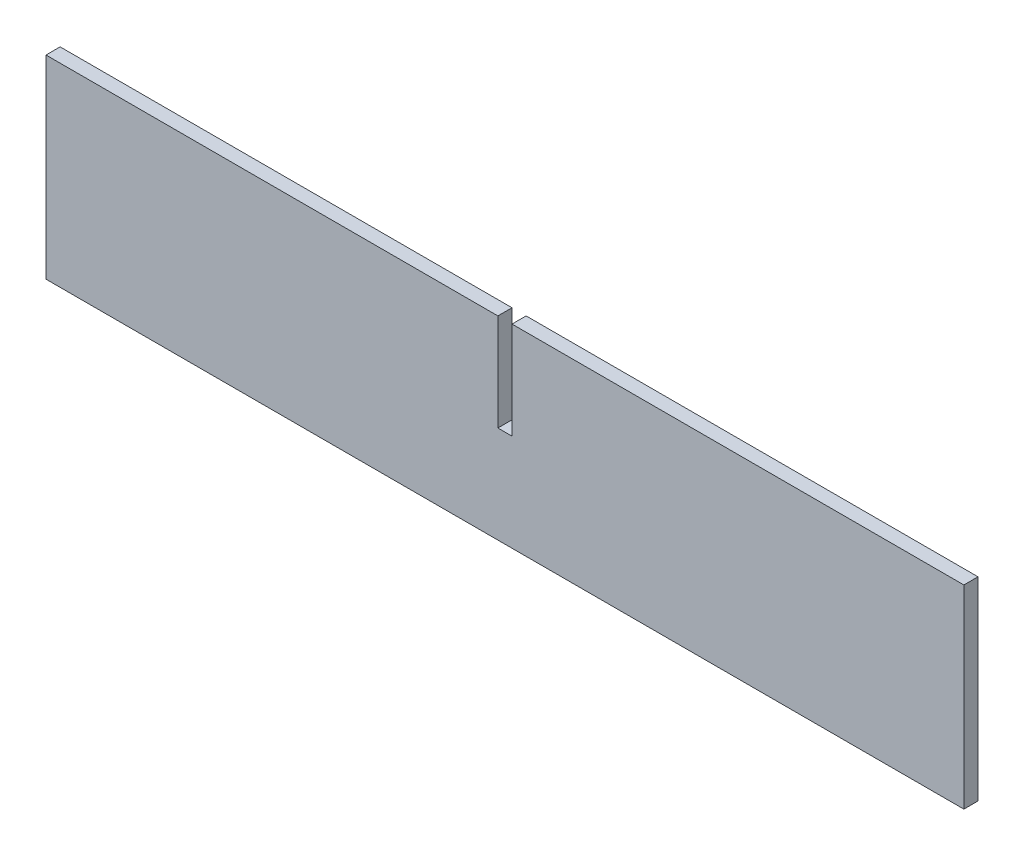
SolidWorks part; units mm, degrees
material "Acrylic (Medium-high impact)"
ref_plane "Front Plane" through (0, 0, 0) normal (0, 0, 1) x (1, 0, 0)
ref_plane "Top Plane" through (0, 0, 0) normal (0, 1, 0) x (1, 0, 0)
ref_plane "Right Plane" through (0, 0, 0) normal (1, 0, 0) x (0, 0, -1)
sketch "Sketch2" plane through (0, 0, 0) normal (0, 0, 1) x (1, 0, 0)
  line L0 (0, 0) -> (0, 137.5) construction
  line L1 (-650, 137.5) -> (-10, 137.5)
  line L2 (-650, 137.5) -> (-650, -137.5)
  line L3 (-650, -137.5) -> (650, -137.5)
  line L4 (650, 137.5) -> (650, -137.5)
  line L5 (-650, 137.5) -> (650, -137.5) construction
  line L6 (-650, -137.5) -> (650, 137.5) construction
  line L7 (10, 0) -> (10, 137.5)
  line L8 (-10, 0) -> (-10, 137.5)
  line L9 (-10, 0) -> (10, 0)
  line L10 (10, 137.5) -> (650, 137.5)
  point P0 (0, 0)
  dimension "D1" = 1300
  dimension "D4" = 275
  dimension "D2" = 10
  dimension "D3" = 10
extrude "Boss-Extrude1" add sketch "Sketch2" along normal blind 20
